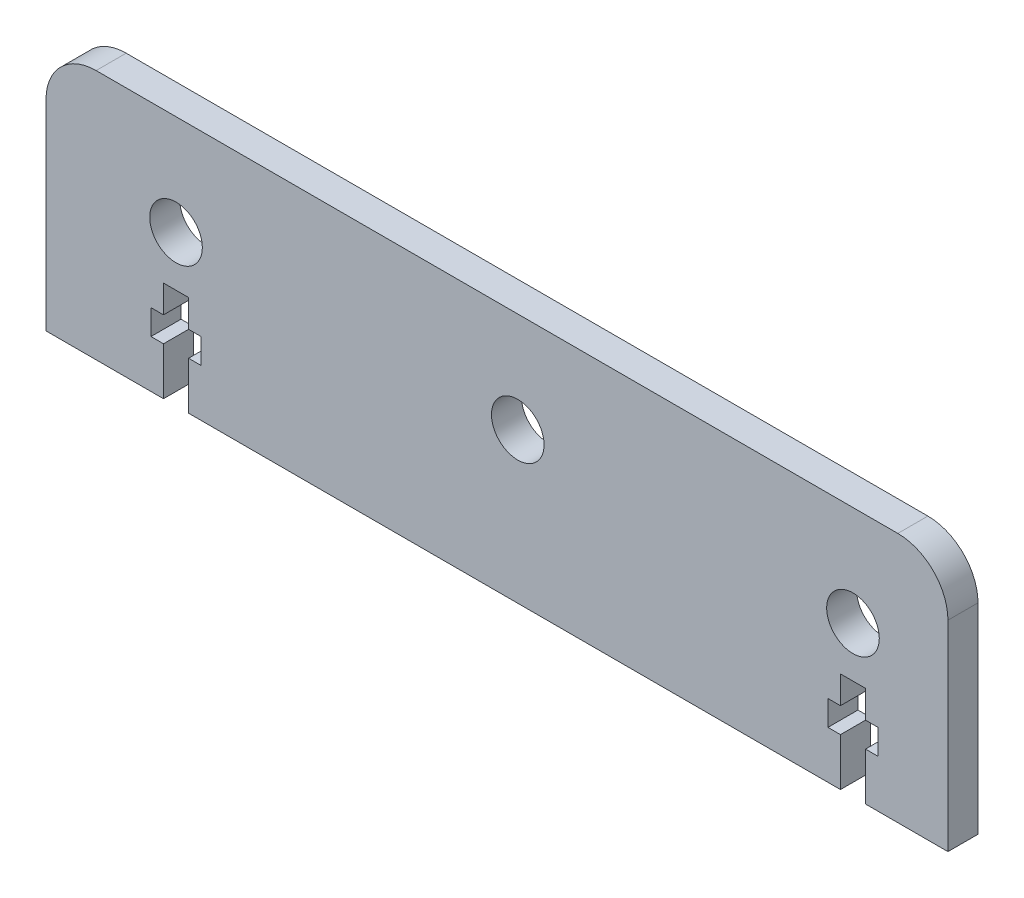
SolidWorks part; units mm, degrees
material "Pine"
ref_plane "Front Plane" through (0, 0, 0) normal (0, 0, 1) x (1, 0, 0)
ref_plane "Top Plane" through (0, 0, 0) normal (0, 1, 0) x (1, 0, 0)
ref_plane "Right Plane" through (0, 0, 0) normal (1, 0, 0) x (0, 0, -1)
sketch "Sketch1" plane through (0, 0, 0) normal (0, 0, 1) x (1, 0, 0)
  line L1 (90, -25) -> (-90, -25)
  line L2 (90, -25) -> (90, 25)
  line L3 (90, 25) -> (-90, 25)
  line L4 (-90, -25) -> (-90, 25)
  line L5 (90, -25) -> (-90, 25) construction
  line L6 (90, 25) -> (-90, -25) construction
  point P0 (0, 0)
  dimension "D1" = 180
  dimension "D2" = 50
extrude "Boss-Extrude1" add sketch "Sketch1" along normal blind 6
sketch "Sketch2" plane through (0, 0, 6) normal (0, 0, 1) x (1, 0, 0)
  line L0 (-90, -25) -> (90, -25) construction
  line L1 (71.05, 27.9939) -> (71.05, -31.0061) construction
  line L2 (4.15, 36.8115) -> (4.15, -31.0061) construction
  line L3 (-64.05, 36.8115) -> (-64.05, -31.0061) construction
  line L4 (90, -25) -> (90, 25) construction
  line L5 (-90, 25) -> (-90, -25) construction
  circle A0 centre (-64.05, 5) radius 5.25
  circle A1 centre (4.15, 5) radius 5.25
  circle A2 centre (71.05, 5) radius 5.25
  dimension "D1" = 30
  dimension "D2" = 10.5
  dimension "D3" = 25.95
  dimension "D5" = 18.95
  dimension "D6" = 66.9
extrude "Cut-Extrude1" cut sketch "Sketch2" against normal through all
fillet "Fillet1" radius 10 2 edges at (90, 25, 3) (-90, 25, 3)
sketch "Sketch3" plane through (0, 0, 0) normal (0, 0, -1) x (-1, 0, 0)
  line L0 (-71.05, 5) -> (-71.05, -35) construction
  line L1 (64.05, 5) -> (64.05, -37.9308) construction
  line L2 (90, -25) -> (-90, -25) construction
  line L3 (-73.55, -5) -> (-68.55, -5)
  line L4 (-73.55, -5) -> (-73.55, -25)
  line L5 (-73.55, -25) -> (-68.55, -25)
  line L6 (-68.55, -5) -> (-68.55, -25)
  line L7 (-73.55, -5) -> (-68.55, -25) construction
  line L8 (-73.55, -25) -> (-68.55, -5) construction
  line L10 (66.55, -5) -> (61.55, -5)
  line L11 (66.55, -5) -> (66.55, -25)
  line L12 (66.55, -25) -> (61.55, -25)
  line L13 (61.55, -5) -> (61.55, -25)
  line L14 (66.55, -5) -> (61.55, -25) construction
  line L15 (66.55, -25) -> (61.55, -5) construction
  line L16 (-66.05, -10.5) -> (-76.05, -10.5)
  line L17 (-66.05, -10.5) -> (-66.05, -15.5)
  line L18 (-66.05, -15.5) -> (-76.05, -15.5)
  line L19 (-76.05, -10.5) -> (-76.05, -15.5)
  line L20 (-66.05, -10.5) -> (-76.05, -15.5) construction
  line L21 (-66.05, -15.5) -> (-76.05, -10.5) construction
  line L22 (69.05, -10.5) -> (59.05, -10.5)
  line L23 (69.05, -10.5) -> (69.05, -15.5)
  line L24 (69.05, -15.5) -> (59.05, -15.5)
  line L25 (59.05, -10.5) -> (59.05, -15.5)
  line L26 (69.05, -10.5) -> (59.05, -15.5) construction
  line L27 (69.05, -15.5) -> (59.05, -10.5) construction
  point P6 (-71.05, -15)
  point P13 (64.05, -15)
  point P18 (-71.05, -13)
  point P23 (64.05, -13)
  dimension "D1" = 20
  dimension "D2" = 5
  dimension "D3" = 12
  dimension "D4" = 5
  dimension "D5" = 10
extrude "Cut-Extrude2" cut sketch "Sketch3" against normal through all contours L6 L5 L4 L3 | L17 L18 L19 L16 | L11 L12 L13 L10 | L23 L24 L25 L22
